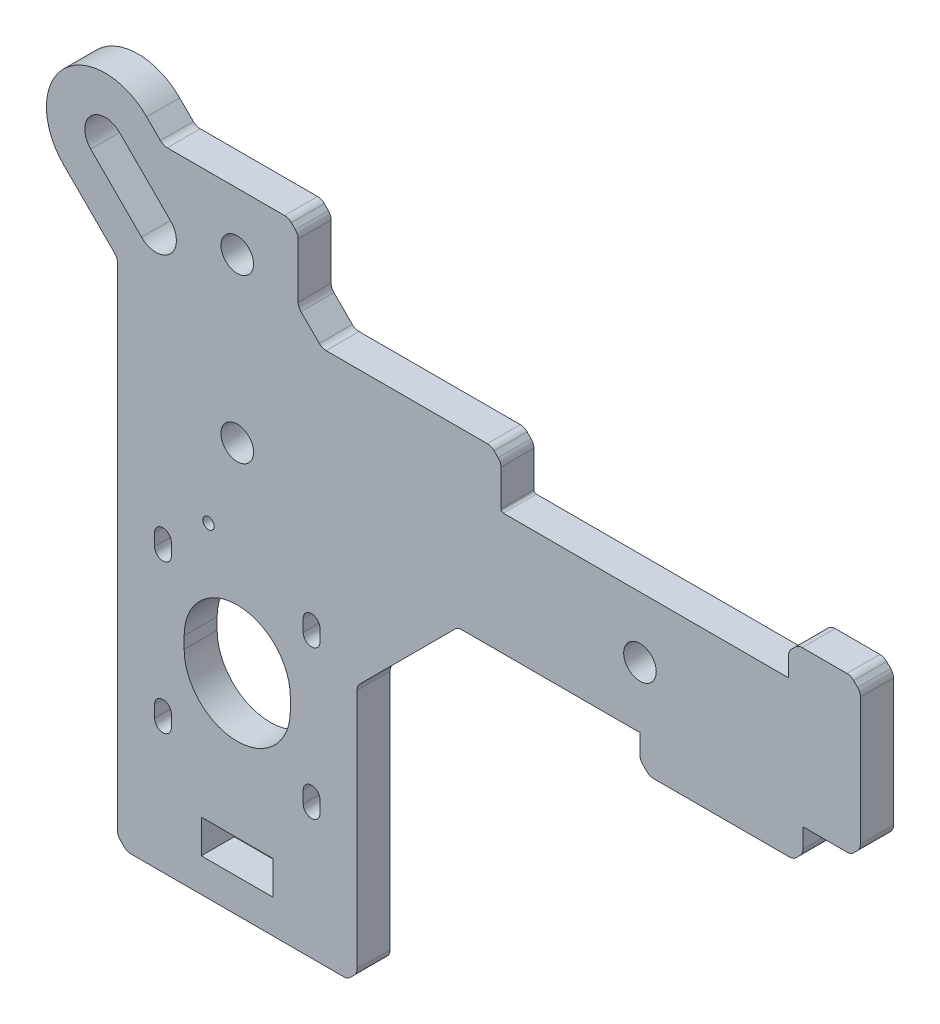
SolidWorks part; units mm, degrees
ref_plane "Front Plane" through (0, 0, 0) normal (0, 0, 1) x (1, 0, 0)
ref_plane "Top Plane" through (0, 0, 0) normal (0, 1, 0) x (1, 0, 0)
ref_plane "Right Plane" through (0, 0, 0) normal (1, 0, 0) x (0, 0, -1)
sketch "Sketch1" plane through (0, 0, 0) normal (0, 0, 1) x (1, 0, 0)
  line L1 (25, -65.675) -> (-25, -65.675)
  line L2 (25, -65.675) -> (25, 65.675)
  line L3 (25, 65.675) -> (-25, 65.675)
  line L4 (-25, -65.675) -> (-25, 65.675)
  line L5 (25, -65.675) -> (-25, 65.675) construction
  line L6 (25, 65.675) -> (-25, -65.675) construction
  point P0 (0, 0)
  dimension "D1" = 50
  dimension "D2" = 131.35
extrude "Boss-Extrude1" add sketch "Sketch1" along normal blind 6.88
sketch "Sketch2" plane through (0, 0, 6.88) normal (0, 0, 1) x (1, 0, 0)
  line L1 (15.5, -36.175) -> (-15.5, -36.175) construction
  line L2 (15.5, -36.175) -> (15.5, -5.175) construction
  line L3 (15.5, -5.175) -> (-15.5, -5.175) construction
  line L4 (-15.5, -36.175) -> (-15.5, -5.175) construction
  line L5 (15.5, -36.175) -> (-15.5, -5.175) construction
  line L6 (15.5, -5.175) -> (-15.5, -36.175) construction
  line L7 (-25, -65.675) -> (25, -65.675) construction
  line L8 (25, 65.675) -> (-25, 65.675) construction
  circle A0 centre (0, -20.675) radius 11.075
  circle A1 centre (-15.5, -5.175) radius 1.75
  circle A2 centre (-15.5, -36.175) radius 1.75
  circle A3 centre (15.5, -36.175) radius 1.75
  circle A4 centre (15.5, -5.175) radius 1.75
  circle A5 centre (0, 53.675) radius 3.4
  circle A6 centre (0, 19.675) radius 3.4
  dimension "D3" = 3.5
  dimension "D4" = 22.15
  dimension "D7" = 6.8
  dimension "D1" = 31
  dimension "D2" = 45
  dimension "D5" = 34
  dimension "D6" = 12
extrude "Cut-Extrude1" cut sketch "Sketch2" against normal through all
sketch "Sketch3" plane through (0, 0, 6.88) normal (0, 0, 1) x (1, 0, 0)
  line L0 (-25, -65.675) -> (25, -65.675) construction
  line L1 (7.5, -51.675) -> (-7.5, -51.675)
  line L2 (7.5, -51.675) -> (7.5, -58.675)
  line L3 (7.5, -58.675) -> (-7.5, -58.675)
  line L4 (-7.5, -51.675) -> (-7.5, -58.675)
  line L5 (7.5, -51.675) -> (-7.5, -58.675) construction
  line L6 (7.5, -58.675) -> (-7.5, -51.675) construction
  point P0 (0, -55.175)
  dimension "D1" = 15
  dimension "D2" = 7
  dimension "D3" = 7
extrude "Cut-Extrude2" cut sketch "Sketch3" against normal blind 6.88
sketch "Sketch4" plane through (0, 0, 6.88) normal (0, 0, 1) x (1, 0, 0)
  line L0 (25, 9.325) -> (130, 9.325)
  line L1 (25, -65.675) -> (25, 65.675) construction
  line L2 (130, 9.325) -> (130, 34.725)
  line L3 (130, 34.725) -> (25, 34.725)
  line L4 (25, 34.725) -> (25, 9.325)
  line L5 (-25, 65.675) -> (-25, -65.675) construction
  line L6 (130, 22.025) -> (0, 22.025) construction
  line L7 (-25, -65.675) -> (25, -65.675) construction
  dimension "D1" = 25.4
  dimension "D2" = 155
  dimension "D3" = 75
extrude "Boss-Extrude2" add sketch "Sketch4" against normal up to vertex (6.88 mm away)
sketch "Sketch5" plane through (0, 0, 6.88) normal (0, 0, 1) x (1, 0, 0)
  line L0 (118, 22.025) -> (84, 22.025) construction
  line L1 (84, 22.025) -> (0, 22.025) construction
  line L2 (130, 9.325) -> (130, 34.725) construction
  circle A0 centre (118, 22.025) radius 3.4
  circle A1 centre (84, 22.025) radius 3.4
  point P8 (130, 22.025)
  dimension "D3" = 6.8
  dimension "D1" = 12
  dimension "D2" = 34
extrude "Cut-Extrude3" cut sketch "Sketch5" against normal blind 6.88
sketch "Sketch6" plane through (0, 0, 6.88) normal (0, 0, 1) x (1, 0, 0)
  line L0 (25, 9.325) -> (130, 9.325) construction
  line L1 (84, 9.325) -> (118, 9.325)
  line L2 (84, 9.325) -> (84, 2.445)
  line L3 (84, 2.445) -> (118, 2.445)
  line L4 (118, 9.325) -> (118, 2.445)
  line L5 (84, 34.725) -> (84, 9.325) construction
  line L6 (118, 22.025) -> (118, 9.325) construction
  line L7 (130, 34.725) -> (25, 34.725) construction
  line L8 (130, 34.725) -> (115, 34.725)
  line L9 (130, 34.725) -> (130, 41.605)
  line L10 (130, 41.605) -> (115, 41.605)
  line L11 (115, 34.725) -> (115, 41.605)
  dimension "D1" = 6.88
  dimension "D2" = 15
  dimension "D3" = 34
extrude "Boss-Extrude3" add sketch "Sketch6" against normal up to vertex (6.88 mm away)
sketch "Sketch7" plane through (0, 0, 6.88) normal (0, 0, 1) x (1, 0, 0)
  line L0 (-25, 65.675) -> (-25, -65.675) construction
  line L5 (115, 34.725) -> (25, 34.725) construction
  line L8 (-25, 65.675) -> (-12.7, 65.675)
  line L9 (-25, 65.675) -> (-25, 45.605)
  line L10 (-25, 45.605) -> (-12.7, 45.605)
  line L11 (-12.7, 65.675) -> (-12.7, 45.605)
  line L12 (25, 65.675) -> (12.7, 65.675)
  line L13 (25, 65.675) -> (25, 45.605)
  line L14 (25, 45.605) -> (12.7, 45.605)
  line L15 (12.7, 65.675) -> (12.7, 45.605)
  dimension "D1" = 25.4
  dimension "D2" = 10.88
extrude "Cut-Extrude4" cut sketch "Sketch7" against normal blind 6.88
sketch "Sketch8" plane through (0, 0, 6.88) normal (0, 0, 1) x (1, 0, 0)
  line L0 (-6, 2.175) -> (6, 2.175) construction
  line L1 (12.7, 65.675) -> (-12.7, 65.675) construction
  line L2 (130, 9.325) -> (130, 41.605) construction
  line L3 (41.1, 28.025) -> (41.1, 16.025) construction
  line L4 (41.1, 22.025) -> (118, 22.025) construction
  circle A0 centre (-6, 2.175) radius 1.1811
  circle A1 centre (6, 2.175) radius 1.1811 construction
  circle A2 centre (41.1, 28.025) radius 1.1811 construction
  circle A3 centre (41.1, 16.025) radius 1.1811 construction
  point P4 (0, 2.175)
  dimension "D1" = 2.3622
  dimension "D2" = 12
  dimension "D3" = 63.5
  dimension "D4" = 12
  dimension "D5" = 88.9
extrude "Cut-Extrude5" cut sketch "Sketch8" against normal blind 6.88
sketch "Sketch9" plane through (0, 0, 6.88) normal (0, 0, 1) x (1, 0, 0)
  circle A0 centre (15.5, -36.175) radius 3
  circle A1 centre (-15.5, -36.175) radius 3
  circle A2 centre (-15.5, -5.175) radius 3
  circle A4 centre (15.5, -5.175) radius 3
  dimension "D1" = 6
extrude "Cut-Extrude6" [suppressed] cut sketch "Sketch9" against normal blind 6.88
sketch "Sketch10" plane through (0, 0, 6.88) normal (0, 0, 1) x (1, 0, 0)
  circle A0 centre (0, -20.675) radius 13
  dimension "D1" = 26
extrude "Boss-Extrude4" [suppressed] add sketch "Sketch10" against normal up to vertex
sketch "Sketch11" plane through (0, 0, 6.88) normal (0, 0, 1) x (1, 0, 0)
  line L0 (115, 34.725) -> (25, 34.725) construction
  line L1 (25, 45.605) -> (55, 45.605)
  line L2 (25, 45.605) -> (25, 34.725)
  line L3 (25, 34.725) -> (55, 34.725)
  line L4 (55, 45.605) -> (55, 34.725)
  dimension "D1" = 30
extrude "Boss-Extrude5" add sketch "Sketch11" against normal up to vertex (6.88 mm away)
chamfer "Chamfer2" distance 21 angle 45 1 edges at (25, 9.325, 3.44)
sketch "Sketch12" plane through (0, 0, 6.88) normal (0, 0, 1) x (1, 0, 0)
  line L0 (-15.5, -5.175) -> (-15.5, -7.675) construction
  line L1 (-13.75, -5.175) -> (-13.75, -7.675)
  line L2 (-17.25, -5.175) -> (-17.25, -7.675)
  line L3 (15.5, -5.175) -> (15.5, -7.675) construction
  line L4 (17.25, -5.175) -> (17.25, -7.675)
  line L5 (13.75, -5.175) -> (13.75, -7.675)
  line L6 (-15.5, -36.175) -> (-15.5, -38.675) construction
  line L7 (-13.75, -36.175) -> (-13.75, -38.675)
  line L8 (-17.25, -36.175) -> (-17.25, -38.675)
  line L9 (15.5, -36.175) -> (15.5, -38.675) construction
  line L10 (17.25, -36.175) -> (17.25, -38.675)
  line L11 (13.75, -36.175) -> (13.75, -38.675)
  line L12 (0, -20.675) -> (0, -23.175) construction
  line L13 (11.075, -20.675) -> (11.075, -23.175)
  line L14 (-11.075, -20.675) -> (-11.075, -23.175)
  arc A0 (-13.75, -5.175) -> (-17.25, -5.175) centre (-15.5, -5.175) ccw
  arc A1 (-17.25, -7.675) -> (-13.75, -7.675) centre (-15.5, -7.675) ccw
  circle A2 centre (-15.5, -5.175) radius 1.75 construction
  arc A3 (17.25, -5.175) -> (13.75, -5.175) centre (15.5, -5.175) ccw
  arc A4 (13.75, -7.675) -> (17.25, -7.675) centre (15.5, -7.675) ccw
  arc A5 (-13.75, -36.175) -> (-17.25, -36.175) centre (-15.5, -36.175) ccw
  arc A6 (-17.25, -38.675) -> (-13.75, -38.675) centre (-15.5, -38.675) ccw
  arc A7 (17.25, -36.175) -> (13.75, -36.175) centre (15.5, -36.175) ccw
  arc A8 (13.75, -38.675) -> (17.25, -38.675) centre (15.5, -38.675) ccw
  arc A9 (11.075, -20.675) -> (-11.075, -20.675) centre (0, -20.675) ccw
  arc A10 (-11.075, -23.175) -> (11.075, -23.175) centre (0, -23.175) ccw
  circle A11 centre (0, -20.675) radius 11.075 construction
  point P3 (-15.5, -6.425)
  point P12 (15.5, -6.425)
  point P19 (-15.5, -37.425)
  point P26 (15.5, -37.425)
  point P35 (0, -21.925)
  dimension "D1" = 2.5
  dimension "D2" = 2.5
extrude "Cut-Extrude7" cut sketch "Sketch12" against normal blind 10
sketch "Sketch13" [suppressed] plane through (0, 0, 6.88) normal (0, 0, 1) x (1, 0, 0)
  line L0 (-15.5, -5.175) -> (-15.5, -7.675) construction
  line L1 (-12.5, -5.175) -> (-12.5, -7.675)
  line L2 (-18.5, -5.175) -> (-18.5, -7.675)
  line L3 (15.5, -5.175) -> (15.5, -7.675) construction
  line L4 (18.5, -5.175) -> (18.5, -7.675)
  line L5 (12.5, -5.175) -> (12.5, -7.675)
  line L6 (15.5, -36.175) -> (15.5, -38.675) construction
  line L7 (18.5, -36.175) -> (18.5, -38.675)
  line L8 (12.5, -36.175) -> (12.5, -38.675)
  line L9 (-15.5, -36.175) -> (-15.5, -38.675) construction
  line L10 (-12.5, -36.175) -> (-12.5, -38.675)
  line L11 (-18.5, -36.175) -> (-18.5, -38.675)
  arc A0 (-12.5, -5.175) -> (-18.5, -5.175) centre (-15.5, -5.175) ccw
  arc A1 (-18.5, -7.675) -> (-12.5, -7.675) centre (-15.5, -7.675) ccw
  circle A2 centre (-15.5, -5.175) radius 3 construction
  arc A3 (18.5, -5.175) -> (12.5, -5.175) centre (15.5, -5.175) ccw
  arc A4 (12.5, -7.675) -> (18.5, -7.675) centre (15.5, -7.675) ccw
  arc A5 (18.5, -36.175) -> (12.5, -36.175) centre (15.5, -36.175) ccw
  arc A6 (12.5, -38.675) -> (18.5, -38.675) centre (15.5, -38.675) ccw
  arc A7 (-12.5, -36.175) -> (-18.5, -36.175) centre (-15.5, -36.175) ccw
  arc A8 (-18.5, -38.675) -> (-12.5, -38.675) centre (-15.5, -38.675) ccw
  point P3 (-15.5, -6.425)
  point P12 (15.5, -6.425)
  point P19 (15.5, -37.425)
  point P26 (-15.5, -37.425)
  dimension "D1" = 2.5
extrude "Cut-Extrude8" [suppressed] cut sketch "Sketch13" against normal blind 10
sketch "Sketch14" [suppressed] plane through (0, 0, 6.88) normal (0, 0, 1) x (1, 0, 0)
  line L0 (3.5, -7) -> (-3.5, -7) construction
  line L1 (3.5, -9) -> (-3.5, -9) construction
  line L2 (3.5, -5) -> (-3.5, -5) construction
  line L3 (-3.5, -3.5) -> (-3.5, -10.5) construction
  line L4 (-1.5, -3.5) -> (-1.5, -10.5)
  line L5 (-5.5, -3.5) -> (-5.5, -10.5)
  line L6 (3.5, -3.5) -> (3.5, -10.5) construction
  line L7 (5.5, -3.5) -> (5.5, -10.5)
  line L8 (1.5, -3.5) -> (1.5, -10.5)
  arc A0 (3.5, -9) -> (3.5, -5) centre (3.5, -7) ccw construction
  arc A1 (-3.5, -5) -> (-3.5, -9) centre (-3.5, -7) ccw construction
  arc A2 (-1.5, -3.5) -> (-5.5, -3.5) centre (-3.5, -3.5) ccw
  arc A3 (-5.5, -10.5) -> (-1.5, -10.5) centre (-3.5, -10.5) ccw
  arc A4 (5.5, -3.5) -> (1.5, -3.5) centre (3.5, -3.5) ccw
  arc A5 (1.5, -10.5) -> (5.5, -10.5) centre (3.5, -10.5) ccw
  point P2 (0, -7)
  point P10 (-3.5, -7)
  point P16 (3.5, -7)
  dimension "D1" = 4
  dimension "D2" = 7
  dimension "D3" = 7
extrude "Cut-Extrude9" [suppressed] cut sketch "Sketch14" against normal through all
chamfer "Chamfer5" distance 5 angle 45 2 edges at (-12.7, 45.605, 3.44) (12.7, 45.605, 3.44)
chamfer "Chamfer3" distance 2 angle 45 11 edges at (-25, -65.675, 3.44) (84, 2.445, 3.44) (118, 2.445, 3.44) (130, 9.325, 3.44) (115, 41.605, 3.44) (130, 41.605, 3.44) (-25, 45.605, 3.44) (-12.7, 65.675, 3.44) (12.7, 65.675, 3.44) (55, 45.605, 3.44) (25, -65.675, 3.44)
sketch "Sketch15" [suppressed] plane through (0, 0, 6.88) normal (0, 0, 1) x (1, 0, 0)
  circle A0 centre (84, 22.025) radius 7.2715
extrude "Boss-Extrude6" [suppressed] add sketch "Sketch15" against normal up to vertex
sketch "Sketch16" plane through (0, 0, 6.88) normal (0, 0, 1) x (1, 0, 0)
  circle A0 centre (118, 22.025) radius 7.069
extrude "Boss-Extrude7" add sketch "Sketch16" against normal up to vertex (6.88 mm away)
sketch "Sketch17" plane through (0, 0, 0) normal (0, 0, 1) x (1, 0, 0)
  line L0 (-16.95, 49.855) -> (-27.5566, 60.4616) construction
  line L2 (-15.2, 48.105) -> (-16.95, 49.855) construction
  line L5 (-12.7, 50.605) -> (-17.7, 45.605) construction
  line L48 (-12.7, 50.605) -> (-12.7, 63.675) construction
  line L54 (-25.6121, 41.1929) -> (-36.2187, 51.7995)
  line L55 (-8.2879, 58.5171) -> (-18.8945, 69.1237)
  line L56 (-27.5566, 60.4616) -> (-16.95, 49.855) construction
  line L57 (-24.5514, 63.4668) -> (-13.9448, 52.8602)
  line L58 (-30.5618, 57.4564) -> (-19.9552, 46.8498)
  line L59 (-10.7, 65.675) -> (-15.4459, 65.675)
  arc A8 (-25.6121, 41.1929) -> (-8.2879, 58.5171) centre (-16.95, 49.855) ccw
  arc A9 (-18.8945, 69.1237) -> (-36.2187, 51.7995) centre (-27.5566, 60.4616) ccw
  arc A10 (-24.5514, 63.4668) -> (-30.5618, 57.4564) centre (-27.5566, 60.4616) ccw
  arc A11 (-19.9552, 46.8498) -> (-13.9448, 52.8602) centre (-16.95, 49.855) ccw
  point P4 (-22.2533, 55.1583)
  point P9 (-22.2533, 55.1583)
  point P16 (-13.5912, 63.8204)
  dimension "D1" = 8.5
  dimension "D2" = 8
  dimension "D3" = 15
extrude "Cut-Extrude10" cut sketch "Sketch17" along normal blind 10 contours L58 A11 L57 A10
sketch "Sketch18" plane through (0, 0, 0) normal (0, 0, -1) x (-1, 0, 0)
  line L0 (10.7, 65.675) -> (15.4459, 65.675) construction
  line L1 (10.7, 65.675) -> (15.4459, 65.675)
  line L2 (24.5514, 63.4668) -> (13.9448, 52.8602)
  line L3 (19.9552, 46.8498) -> (30.5618, 57.4564)
  line L4 (24.5514, 63.4668) -> (13.9448, 52.8602)
  line L5 (19.9552, 46.8498) -> (30.5618, 57.4564)
  line L6 (25.6121, 41.1929) -> (36.2187, 51.7995)
  line L7 (18.8945, 69.1237) -> (8.2879, 58.5171)
  line L8 (25.6121, 41.1929) -> (36.2187, 51.7995)
  line L9 (18.8945, 69.1237) -> (15.4459, 65.675)
  line L10 (10.7, 65.675) -> (10.7, 60.9291)
  line L11 (10.7, 60.9291) -> (8.2879, 58.5171)
  arc A2 (13.9448, 52.8602) -> (19.9552, 46.8498) centre (16.95, 49.855) ccw
  arc A3 (30.5618, 57.4564) -> (24.5514, 63.4668) centre (27.5566, 60.4616) ccw
  arc A4 (13.9448, 52.8602) -> (19.9552, 46.8498) centre (16.95, 49.855) ccw
  arc A5 (30.5618, 57.4564) -> (24.5514, 63.4668) centre (27.5566, 60.4616) ccw
  arc A6 (36.2187, 51.7995) -> (18.8945, 69.1237) centre (27.5566, 60.4616) ccw
  arc A7 (8.2879, 58.5171) -> (25.6121, 41.1929) centre (16.95, 49.855) ccw
  arc A8 (36.2187, 51.7995) -> (18.8945, 69.1237) centre (27.5566, 60.4616) ccw
  arc A9 (8.2879, 58.5171) -> (25.6121, 41.1929) centre (16.95, 49.855) ccw
  dimension "D1" = 0
  dimension "D2" = 0
extrude "Boss-Extrude8" add sketch "Sketch18" against normal up to vertex (6.88 mm away)
fillet "Fillet1" radius 2 24 edges at (-25, -63.675, 3.44) (-23, -65.675, 3.44) (23, -65.675, 3.44) (25, -63.675, 3.44) (25, -11.675, 3.44) (46, 9.325, 3.44) (84, 4.445, 3.44) (86, 2.445, 3.44) (116, 2.445, 3.44) (118, 4.445, 3.44) (128, 9.325, 3.44) (130, 11.325, 3.44) (130, 39.605, 3.44) (128, 41.605, 3.44) (117, 41.605, 3.44) (115, 39.605, 3.44) (55, 43.605, 3.44) (53, 45.605, 3.44) (17.7, 45.605, 3.44) (12.7, 50.605, 3.44) (-15.4459, 65.675, 3.44) (-25, 40.6214, 3.44) (12.7, 63.675, 3.44) (10.7, 65.675, 3.44)
fillet "Fillet2" [suppressed] radius 0.5
fillet "Fillet3" radius 0.5 1 edges at (55, 34.725, 3.44)
sketch "Sketch19" [suppressed] plane through (0, 0, 6.88) normal (0, 0, 1) x (1, 0, 0)
  line L0 (118, 22.025) -> (98, 22.025) construction
  text T0 "Z" font "Comic Sans MS" height 5
  dimension "D1" = 20
extrude "Cut-Extrude11" [suppressed] cut sketch "Sketch19" against normal blind 1
sketch "Sketch20" plane through (0, 0, 0) normal (0, 0, -1) x (-1, 0, 0)
  line L0 (-84, 22.025) -> (-104, 22.025) construction
  text T0 "Z" font "Comic Sans MS" height 5
  dimension "D1" = 20
extrude "Cut-Extrude12" cut sketch "Sketch20" against normal blind 1
